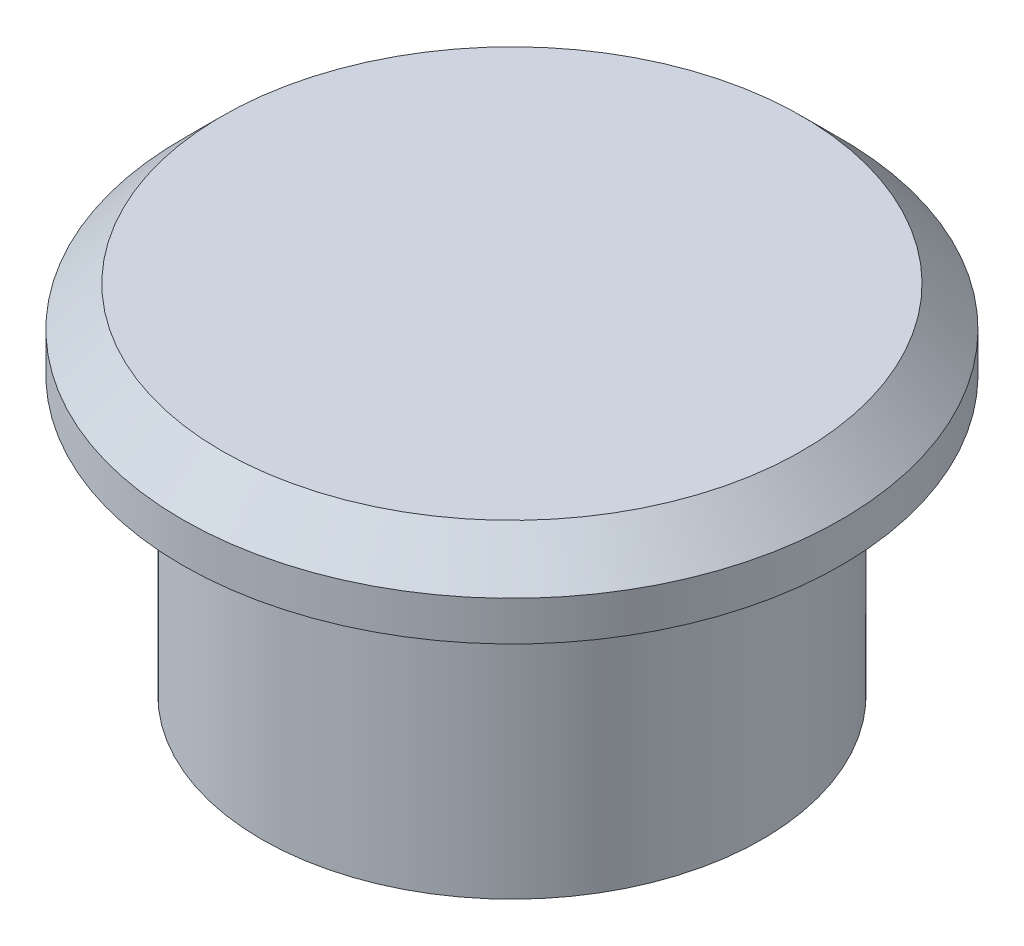
SolidWorks part; units mm, degrees
ref_plane "Front Plane" through (0, 0, 0) normal (0, 0, 1) x (1, 0, 0)
ref_plane "Top Plane" through (0, 0, 0) normal (0, 1, 0) x (1, 0, 0)
ref_plane "Right Plane" through (0, 0, 0) normal (1, 0, 0) x (0, 0, -1)
sketch "Sketch1" plane through (0, 0, 0) normal (0, 1, 0) x (1, 0, 0)
  circle A0 centre (0, 0) radius 6.33
extrude "Boss-Extrude1" add sketch "Sketch1" along normal blind 7
sketch "Sketch2" plane through (0, 7, 0) normal (0, 1, 0) x (1, 0, 0)
  circle A0 centre (0, 0) radius 4.6917
extrude "Cut-Extrude1" cut sketch "Sketch2" against normal blind 7
sketch "Sketch3" plane through (0, 7, 0) normal (0, 1, 0) x (1, 0, 0)
  circle A0 centre (0, 0) radius 8.33
extrude "Boss-Extrude2" add sketch "Sketch3" along normal blind 2
chamfer "Chamfer1" distance 1 angle 45 1 edges at (0, 9, 8.33)
